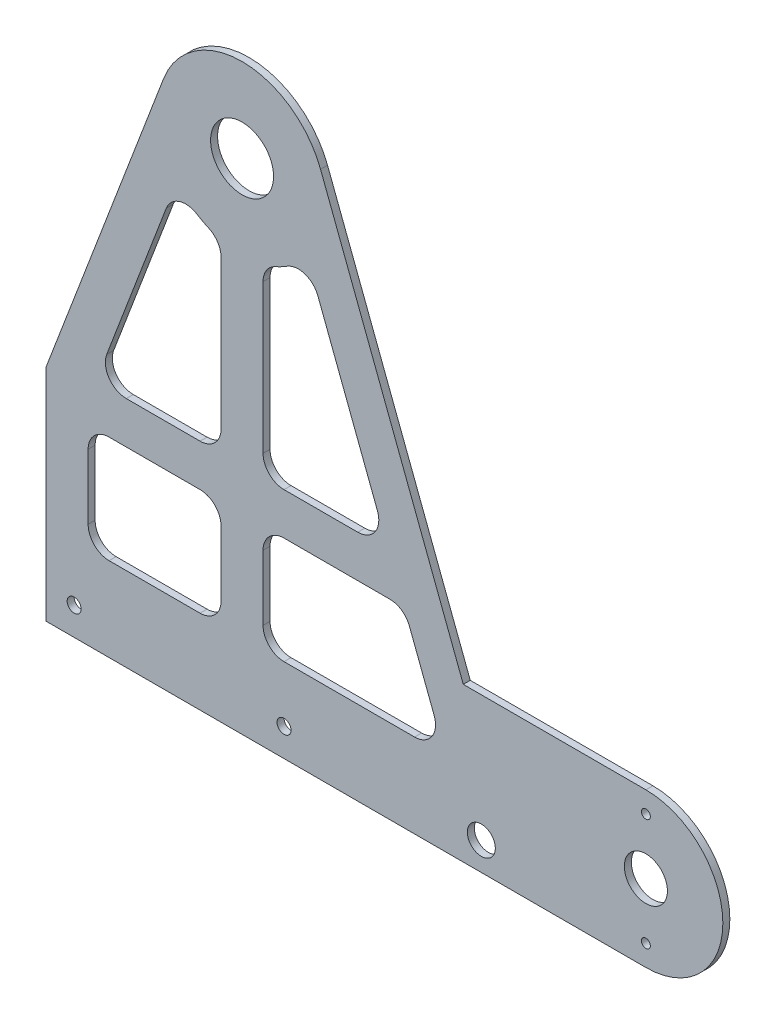
SolidWorks part; units mm, degrees
material "6061-T6 (SS)"
ref_plane "Front Plane" through (0, 0, 0) normal (0, 0, 1) x (1, 0, 0)
ref_plane "Top Plane" through (0, 0, 0) normal (0, 1, 0) x (1, 0, 0)
ref_plane "Right Plane" through (0, 0, 0) normal (1, 0, 0) x (0, 0, -1)
sketch "Sketch1" plane through (0, 0, 0) normal (0, 0, 1) x (1, 0, 0)
  line L0 (-35.604, 119.9573) -> (-127, -119.9573)
  line L1 (-127, -119.9573) -> (127, -119.9573)
  line L2 (127, -119.9573) -> (35.604, 119.9573)
  arc A0 (-35.604, 119.9573) -> (35.604, 119.9573) centre (0, 106.3939) cw
  point P2 (-81.302, 0)
  point P7 (0, 213.4177)
  dimension "D3" = 38.1
  dimension "D1" = 254
  dimension "D2" = 333.375
extrude "Boss-Extrude1" add sketch "Sketch1" along normal blind 3.175
sketch "Sketch2" plane through (0, 0, 3.175) normal (0, 0, 1) x (1, 0, 0)
  circle A0 centre (0, 106.3939) radius 14.2875
  arc A1 (35.604, 119.9573) -> (-35.604, 119.9573) centre (0, 106.3939) ccw construction
  dimension "D1" = 28.575
extrude "Cut-Extrude1" cut sketch "Sketch2" against normal through all contours A0
sketch "Sketch4" plane through (0, 0, 3.175) normal (0, 0, 1) x (1, 0, 0)
  line L0 (120.4396, -102.7361) -> (108.5716, -107.2573) construction
  line L1 (127, -119.9573) -> (35.604, 119.9573) construction
  line L2 (108.5716, -107.2573) -> (108.5716, -119.9573) construction
  line L3 (-127, -119.9573) -> (127, -119.9573) construction
  circle A0 centre (108.5716, -107.2573) radius 6.35
  circle A1 centre (-76.2, -107.2573) radius 3.175
  circle A2 centre (19.05, -107.2573) radius 3.175
  dimension "D1" = 12.7
  dimension "D4" = 95.25
  dimension "D5" = 6.35
  dimension "D2" = 12.7
  dimension "D3" = 12.7
extrude "Cut-Extrude2" cut sketch "Sketch4" against normal through all contours A0
sketch "Sketch7" plane through (0, 0, 3.175) normal (0, 0, 1) x (1, 0, 0)
  line L0 (-127, -119.9573) -> (127, -119.9573) construction
  line L1 (-50.8, -119.9573) -> (50.8, -119.9573)
  line L2 (-50.8, -119.9573) -> (-50.8, -123.1323)
  line L3 (-50.8, -123.1323) -> (50.8, -123.1323)
  line L4 (50.8, -119.9573) -> (50.8, -123.1323)
  line L5 (-50.8, -123.1323) -> (-127, -119.9573) construction
  line L6 (127, -119.9573) -> (50.8, -123.1323) construction
  dimension "D1" = 3.175
  dimension "D2" = 101.6
extrude "Boss-Extrude2" [suppressed] add sketch "Sketch7" against normal blind 3.175 contours L3 L4 L1 L2
sketch "Sketch8" plane through (0, 0, 0) normal (0, 0, -1) x (-1, 0, 0)
  line L1 (0, 106.3939) -> (-183.2513, -85.0323) construction
  line L5 (-127, -119.9573) -> (-183.2513, -119.9573)
  line L6 (-183.2513, -50.1073) -> (-100.3905, -50.1073)
  line L7 (-127, -119.9573) -> (-35.604, 119.9573) construction
  line L8 (-100.3905, -50.1073) -> (-127, -119.9573)
  circle A0 centre (-183.2513, -85.0323) radius 9.779
  arc A2 (-183.2513, -119.9573) -> (-183.2513, -50.1073) centre (-183.2513, -85.0323) cw
  dimension "D1" = 19.558
  dimension "D4" = 34.925
  dimension "D3" = 265
extrude "Boss-Extrude3" add sketch "Sketch8" against normal blind 3.175
sketch "Sketch9" plane through (0, 0, 3.175) normal (0, 0, 1) x (1, 0, 0)
  circle A2 centre (183.2513, -59.6323) radius 2.0193
  circle A3 centre (183.2513, -110.4323) radius 2.0193
  circle A4 centre (183.2513, -110.4323) radius 2.0193 construction
  circle A5 centre (183.2513, -59.6323) radius 2.0193 construction
extrude "Cut-Extrude3" cut sketch "Sketch9" against normal through all
sketch "Sketch10" plane through (0, 0, 3.175) normal (0, 0, 1) x (1, 0, 0)
  line L0 (-35.604, 119.9573) -> (-127, -119.9573) construction
  line L1 (-88.9, -19.9448) -> (-127, -19.9448)
  line L2 (-88.9, -19.9448) -> (-88.9, -119.9573)
  line L3 (-88.9, -119.9573) -> (-127, -119.9573)
  line L4 (-127, -19.9448) -> (-127, -119.9573)
  dimension "D1" = 38.1
extrude "Cut-Extrude4" cut sketch "Sketch10" against normal through all
sketch "Sketch11" plane through (0, 0, 3.175) normal (0, 0, 1) x (1, 0, 0)
  line L3 (9.525, 62.7448) -> (9.525, -4.723) construction
  line L4 (-34.4137, 69.5698) -> (-61.424, -1.3322) construction
  line L5 (-52.523, -14.248) -> (-19.05, -14.248) construction
  line L9 (-9.525, -4.723) -> (-9.525, 62.7448) construction
  line L10 (19.05, -14.248) -> (52.523, -14.248) construction
  line L11 (61.424, -1.3322) -> (34.4137, 69.5698) construction
  line L16 (-34.4137, 69.5698) -> (-61.424, -1.3322)
  line L17 (-52.523, -14.248) -> (-19.05, -14.248)
  line L18 (-9.525, -4.723) -> (-9.525, 62.7448)
  line L19 (19.05, -14.248) -> (52.523, -14.248)
  line L25 (61.424, -1.3322) -> (34.4137, 69.5698)
  line L26 (9.525, 62.7448) -> (9.525, -4.723)
  line L27 (-19.05, -33.298) -> (-60.325, -33.298) construction
  line L28 (-69.85, -42.823) -> (-69.85, -72.3323) construction
  line L29 (-60.325, -81.8573) -> (-19.05, -81.8573) construction
  line L34 (-9.525, -72.3323) -> (-9.525, -42.823) construction
  line L35 (9.525, -42.823) -> (9.525, -72.3323) construction
  line L36 (19.05, -81.8573) -> (78.2789, -81.8573) construction
  line L37 (87.1799, -68.9414) -> (75.9383, -39.4322) construction
  line L41 (67.0373, -33.298) -> (19.05, -33.298) construction
  line L42 (-19.05, -33.298) -> (-60.325, -33.298)
  line L43 (-69.85, -42.823) -> (-69.85, -72.3323)
  line L48 (-60.325, -81.8573) -> (-19.05, -81.8573)
  line L49 (-9.525, -72.3323) -> (-9.525, -42.823)
  line L50 (9.525, -42.823) -> (9.525, -72.3323)
  line L51 (19.05, -81.8573) -> (78.2789, -81.8573)
  line L56 (87.1799, -68.9414) -> (75.9383, -39.4322)
  line L57 (67.0373, -33.298) -> (19.05, -33.298)
  arc A5 (15.24, 71.4746) -> (20.4102, 74.2219) centre (0, 106.3939) ccw construction
  arc A6 (15.24, 71.4746) -> (9.525, 62.7448) centre (19.05, 62.7448) ccw construction
  arc A7 (-61.424, -1.3322) -> (-52.523, -14.248) centre (-52.523, -4.723) ccw construction
  arc A8 (-19.05, -14.248) -> (-9.525, -4.723) centre (-19.05, -4.723) ccw construction
  arc A9 (-9.525, 62.7448) -> (-15.24, 71.4746) centre (-19.05, 62.7448) ccw construction
  arc A15 (-20.4102, 74.2219) -> (-15.24, 71.4746) centre (0, 106.3939) ccw construction
  arc A16 (-20.4102, 74.2219) -> (-34.4137, 69.5698) centre (-25.5127, 66.1789) ccw construction
  arc A17 (9.525, -4.723) -> (19.05, -14.248) centre (19.05, -4.723) ccw construction
  arc A18 (52.523, -14.248) -> (61.424, -1.3322) centre (52.523, -4.723) ccw construction
  arc A19 (34.4137, 69.5698) -> (20.4102, 74.2219) centre (25.5127, 66.1789) ccw construction
  arc A24 (-61.424, -1.3322) -> (-52.523, -14.248) centre (-52.523, -4.723) ccw
  arc A25 (-19.05, -14.248) -> (-9.525, -4.723) centre (-19.05, -4.723) ccw
  arc A26 (-9.525, 62.7448) -> (-15.24, 71.4746) centre (-19.05, 62.7448) ccw
  arc A27 (-20.4102, 74.2219) -> (-15.24, 71.4746) centre (0, 106.3939) ccw
  arc A33 (-20.4102, 74.2219) -> (-34.4137, 69.5698) centre (-25.5127, 66.1789) ccw
  arc A34 (9.525, -4.723) -> (19.05, -14.248) centre (19.05, -4.723) ccw
  arc A35 (52.523, -14.248) -> (61.424, -1.3322) centre (52.523, -4.723) ccw
  arc A36 (34.4137, 69.5698) -> (20.4102, 74.2219) centre (25.5127, 66.1789) ccw
  arc A37 (15.24, 71.4746) -> (20.4102, 74.2219) centre (0, 106.3939) ccw
  arc A42 (15.24, 71.4746) -> (9.525, 62.7448) centre (19.05, 62.7448) ccw
  arc A43 (19.05, -33.298) -> (9.525, -42.823) centre (19.05, -42.823) ccw construction
  arc A44 (-9.525, -42.823) -> (-19.05, -33.298) centre (-19.05, -42.823) ccw construction
  arc A45 (-60.325, -33.298) -> (-69.85, -42.823) centre (-60.325, -42.823) ccw construction
  arc A49 (-69.85, -72.3323) -> (-60.325, -81.8573) centre (-60.325, -72.3323) ccw construction
  arc A50 (-19.05, -81.8573) -> (-9.525, -72.3323) centre (-19.05, -72.3323) ccw construction
  arc A51 (9.525, -72.3323) -> (19.05, -81.8573) centre (19.05, -72.3323) ccw construction
  arc A56 (78.2789, -81.8573) -> (87.1799, -68.9414) centre (78.2789, -72.3323) ccw construction
  arc A57 (75.9383, -39.4322) -> (67.0373, -33.298) centre (67.0373, -42.823) ccw construction
  arc A58 (-9.525, -42.823) -> (-19.05, -33.298) centre (-19.05, -42.823) ccw
  arc A59 (-60.325, -33.298) -> (-69.85, -42.823) centre (-60.325, -42.823) ccw
  arc A64 (-69.85, -72.3323) -> (-60.325, -81.8573) centre (-60.325, -72.3323) ccw
  arc A65 (-19.05, -81.8573) -> (-9.525, -72.3323) centre (-19.05, -72.3323) ccw
  arc A66 (9.525, -72.3323) -> (19.05, -81.8573) centre (19.05, -72.3323) ccw
  arc A67 (78.2789, -81.8573) -> (87.1799, -68.9414) centre (78.2789, -72.3323) ccw
  arc A68 (75.9383, -39.4322) -> (67.0373, -33.298) centre (67.0373, -42.823) ccw
  arc A69 (19.05, -33.298) -> (9.525, -42.823) centre (19.05, -42.823) ccw
extrude "Cut-Extrude5" cut sketch "Sketch11" against normal through all
